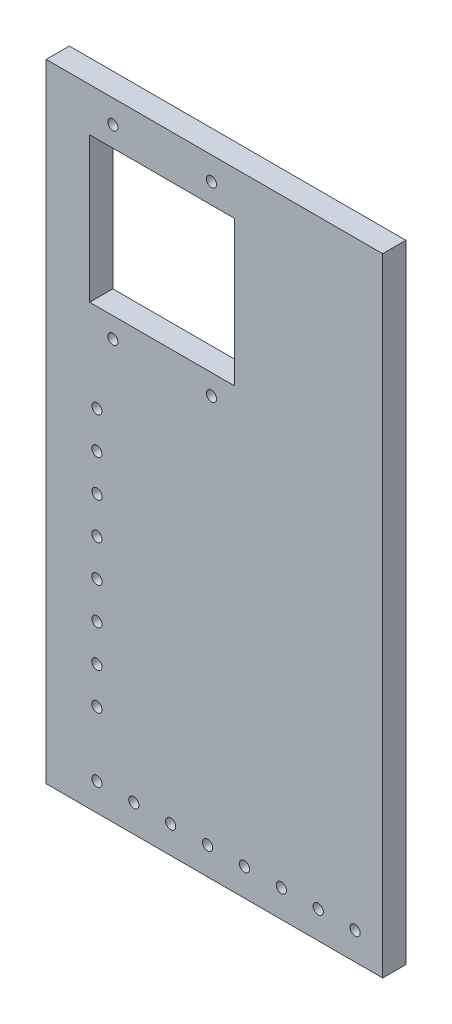
SolidWorks part; units mm, degrees
ref_plane "Plano frontal" through (0, 0, 0) normal (0, 0, 1) x (1, 0, 0)
ref_plane "Plano superior" through (0, 0, 0) normal (0, 1, 0) x (1, 0, 0)
ref_plane "Plano direito" through (0, 0, 0) normal (1, 0, 0) x (0, 0, -1)
sketch "Esboço1" plane through (0, 0, 0) normal (0, 0, 1) x (1, 0, 0)
  line L1 (-25, 25) -> (25, 25)
  line L2 (-25, 25) -> (-25, -25)
  line L3 (-25, -25) -> (25, -25)
  line L4 (25, 25) -> (25, -25)
  line L5 (-25, 25) -> (25, -25) construction
  line L6 (-25, -25) -> (25, 25) construction
  line L7 (-40, 40) -> (76, 40)
  line L8 (-40, 40) -> (-40, -176.23)
  line L9 (-40, -176.23) -> (76, -176.23)
  line L10 (76, 40) -> (76, -176.23)
  line L11 (-40, 40) -> (76, -176.23) construction
  line L12 (-40, -176.23) -> (76, 40) construction
  circle A0 centre (-17, 32) radius 1.75
  circle A1 centre (17, 32) radius 1.75
  circle A2 centre (-17, -32) radius 1.75
  circle A3 centre (17, -32) radius 1.75
  point P8 (0, 0)
  point P14 (18, -68.115)
  dimension "D1" = 3.5
  dimension "D2" = 3.5
  dimension "D3" = 3.5
  dimension "D4" = 3.5
  dimension "D5" = 34
  dimension "D6" = 64
  dimension "D7" = 34
  dimension "D8" = 64
  dimension "D9" = 32
  dimension "D10" = 17
  dimension "D11" = 50
  dimension "D12" = 50
  dimension "D13" = 116
  dimension "D14" = 216.23
  dimension "D15" = 40
  dimension "D16" = 40
extrude "Ressalto-extrusão2" add sketch "Esboço1" along normal blind 8
sketch "Esboço2" plane through (0, 0, 0) normal (0, 0, -1) x (-1, 0, 0)
  line L0 (40, -176.23) -> (-76, -176.23) construction
  line L1 (-76, -176.23) -> (-76, 40) construction
  circle A0 centre (-66.5, -166.73) radius 1.75
  dimension "D1" = 3.5
  dimension "D2" = 9.5
  dimension "D3" = 9.5
extrude "Corte-extrusão1" cut sketch "Esboço2" against normal blind 100
pattern_linear "Padrão linear1" count 8 spacing 12.7143 along (-1, 0, 0) of "Corte-extrusão1"
sketch "Esboço3" plane through (0, 0, 0) normal (0, 0, -1) x (-1, 0, 0)
  line L0 (40, 40) -> (40, -176.23) construction
  line L1 (-76, 40) -> (40, 40) construction
  circle A0 centre (22.5, -55.5) radius 1.75
  dimension "D1" = 3.5
  dimension "D2" = 17.5
  dimension "D3" = 95.5
extrude "Corte-extrusão2" cut sketch "Esboço3" against normal blind 100
pattern_linear "Padrão linear2" count 8 spacing 12.7143 along (0, -1, 0) of "Corte-extrusão2"
